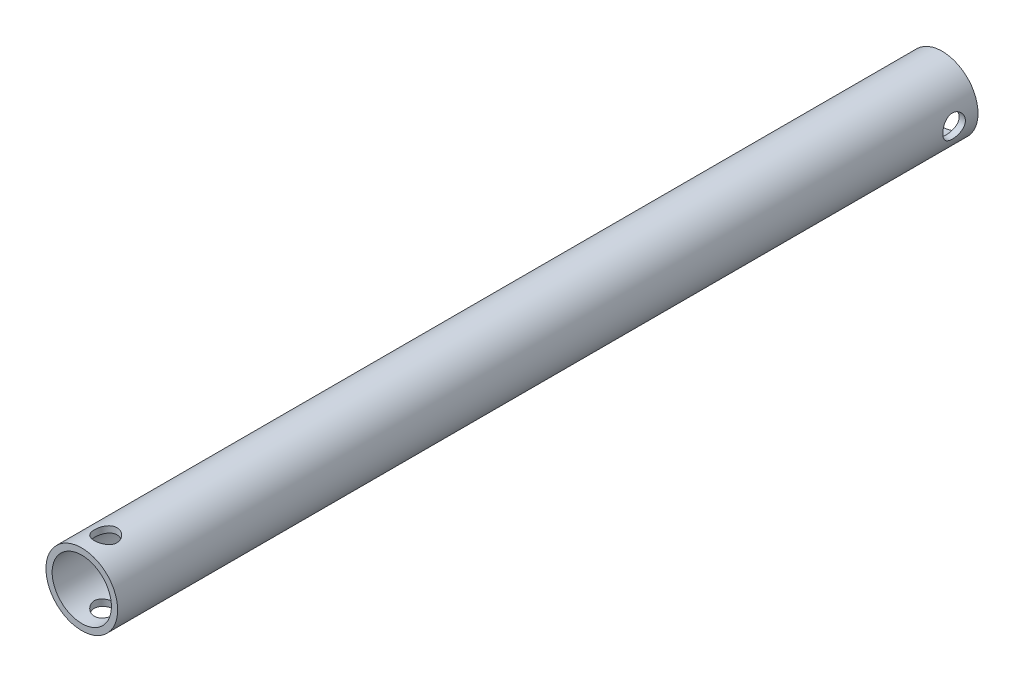
SolidWorks part; units mm, degrees
ref_plane "Front Plane" through (0, 0, 0) normal (0, 0, 1) x (1, 0, 0)
ref_plane "Top Plane" through (0, 0, 0) normal (0, 1, 0) x (1, 0, 0)
ref_plane "Right Plane" through (0, 0, 0) normal (1, 0, 0) x (0, 0, -1)
sketch "Sketch1" plane through (0, 0, 0) normal (0, 0, 1) x (1, 0, 0)
  circle A0 centre (0, 0) radius 9.525
  circle A1 centre (0, 0) radius 7.874
  dimension "D1" = 1.651
extrude "Boss-Extrude1" add sketch "Sketch1" along normal blind 228.6
ref_plane "Plane1" through (0, 9.525, 0) normal (0, 1, 0) x (1, 0, 0)
sketch "Sketch2" plane through (0, 9.525, 0) normal (0, 1, 0) x (1, 0, 0)
  line L0 (-9.525, -114.3) -> (9.525, -114.3) construction
  line L1 (-9.525, 0) -> (-9.525, -228.6) construction
  line L2 (9.525, -228.6) -> (9.525, 0) construction
  line L3 (0, -228.6) -> (0, -222.25) construction
  line L4 (-9.525, -228.6) -> (9.525, -228.6) construction
  circle A0 centre (0, -222.25) radius 3
extrude "Cut-Extrude1" cut sketch "Sketch2" against normal blind 138.8059
ref_plane "Plane2" through (9.525, 0, 0) normal (1, 0, 0) x (0, 0, -1)
sketch "Sketch3" plane through (9.525, 0, 0) normal (1, 0, 0) x (0, 0, -1)
  line L0 (0, 0) -> (-6.35, 0) construction
  circle A0 centre (-6.35, 0) radius 3
extrude "Cut-Extrude2" cut sketch "Sketch3" against normal blind 138.8059
